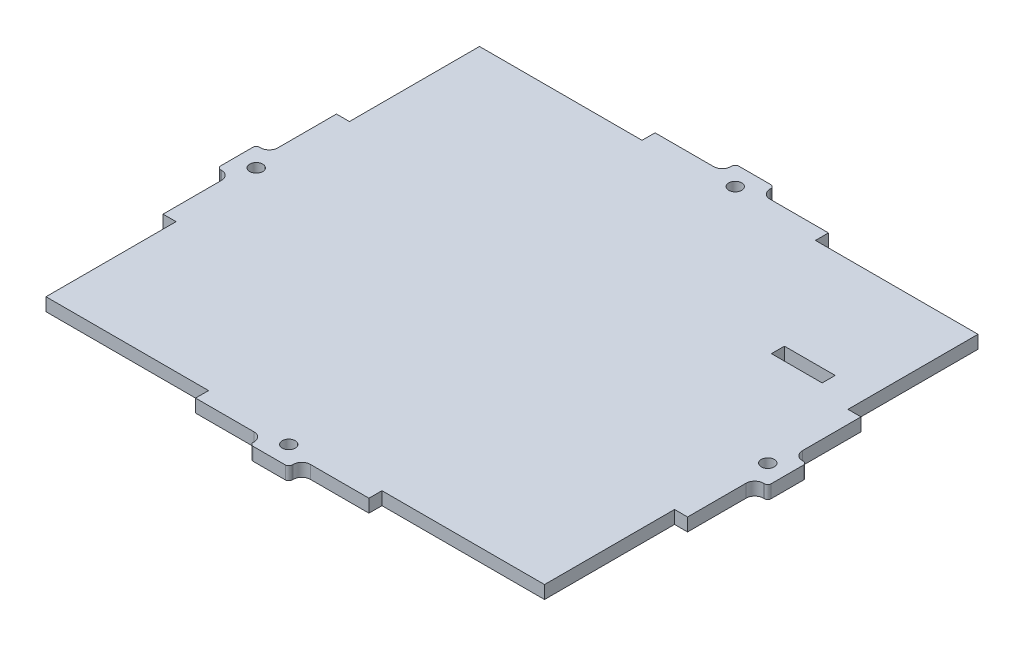
SolidWorks part; units mm, degrees
material "Acrylic (Medium-high impact)"
ref_plane "Plano frontal" through (0, 0, 0) normal (0, 0, 1) x (1, 0, 0)
ref_plane "Plano superior" through (0, 0, 0) normal (0, 1, 0) x (1, 0, 0)
ref_plane "Plano direito" through (0, 0, 0) normal (1, 0, 0) x (0, 0, -1)
sketch "Esboço1" plane through (0, 0, 0) normal (0, 1, 0) x (1, 0, 0)
  line L1 (-57.5, -50) -> (57.5, -50)
  line L2 (-57.5, -50) -> (-57.5, 50)
  line L3 (-57.5, 50) -> (57.5, 50)
  line L4 (57.5, -50) -> (57.5, 50)
  line L5 (-57.5, -50) -> (57.5, 50) construction
  line L6 (-57.5, 50) -> (57.5, -50) construction
  point P0 (0, 0)
  dimension "D1" = 115
  dimension "D2" = 100
extrude "Ressalto-extrusão1" add sketch "Esboço1" along normal mid plane 3
sketch "Esboço4" plane through (0, 1.5, 0) normal (0, 1, 0) x (1, 0, 0)
  line L5 (0, -1.65) -> (0, 1.65) construction
  line L21 (6.5, 53) -> (20, 53)
  line L26 (-3.7, 56) -> (3.7, 56)
  line L27 (-4.5, 55.2) -> (-4.5, 55)
  line L33 (-63.5, 3.7) -> (-63.5, -3.7)
  line L42 (57.5, 50) -> (-57.5, 50) construction
  line L43 (-20, 50) -> (20, 50)
  line L44 (-20, 50) -> (-20, 53)
  line L45 (-20, 53) -> (-6.5, 53)
  line L46 (20, 50) -> (20, 53)
  line L48 (4.5, 55.2) -> (4.5, 55)
  line L49 (-1.65, 0) -> (1.65, 0) construction
  line L50 (4.5, -55.2) -> (4.5, -55)
  line L51 (20, -50) -> (20, -53)
  line L52 (-20, -53) -> (-6.5, -53)
  line L53 (-20, -50) -> (-20, -53)
  line L54 (-20, -50) -> (20, -50)
  line L55 (-4.5, -55.2) -> (-4.5, -55)
  line L56 (-3.7, -56) -> (3.7, -56)
  line L57 (6.5, -53) -> (20, -53)
  line L58 (57.5, -50) -> (57.5, 50) construction
  line L59 (57.5, 20) -> (60.5, 20)
  line L60 (57.5, 20) -> (57.5, -20)
  line L61 (57.5, -20) -> (60.5, -20)
  line L62 (60.5, 20) -> (60.5, 6.5)
  line L63 (60.5, -6.5) -> (60.5, -20)
  line L64 (62.5, 4.5) -> (62.7, 4.5)
  line L66 (62.5, -4.5) -> (62.7, -4.5)
  line L67 (63.5, 3.7) -> (63.5, -3.7)
  line L77 (-62.5, -4.5) -> (-62.7, -4.5)
  line L91 (-62.5, 4.5) -> (-62.7, 4.5)
  line L92 (-60.5, -6.5) -> (-60.5, -20)
  line L93 (-60.5, 20) -> (-60.5, 6.5)
  line L94 (-57.5, -20) -> (-60.5, -20)
  line L95 (-57.5, 20) -> (-57.5, -20)
  line L96 (-57.5, 20) -> (-60.5, 20)
  circle A6 centre (0, 51.5) radius 1.5 construction
  arc A7 (6.5, 53) -> (4.5, 55) centre (6.5, 55) cw
  arc A8 (-4.5, 55) -> (-6.5, 53) centre (-6.5, 55) cw
  circle A9 centre (0, -51.5) radius 1.5 construction
  arc A10 (-4.5, -55) -> (-6.5, -53) centre (-6.5, -55) ccw
  arc A11 (6.5, -53) -> (4.5, -55) centre (6.5, -55) ccw
  arc A12 (60.5, -6.5) -> (62.5, -4.5) centre (62.5, -6.5) cw
  arc A13 (62.5, 4.5) -> (60.5, 6.5) centre (62.5, 6.5) cw
  arc A18 (-62.5, 4.5) -> (-60.5, 6.5) centre (-62.5, 6.5) ccw
  arc A19 (-60.5, -6.5) -> (-62.5, -4.5) centre (-62.5, -6.5) ccw
  arc A20 (-63.5, -3.7) -> (-62.7, -4.5) centre (-62.7, -3.7) ccw
  arc A21 (-63.5, 3.7) -> (-62.7, 4.5) centre (-62.7, 3.7) cw
  arc A22 (-4.5, -55.2) -> (-3.7, -56) centre (-3.7, -55.2) ccw
  arc A23 (4.5, -55.2) -> (3.7, -56) centre (3.7, -55.2) cw
  arc A24 (62.7, -4.5) -> (63.5, -3.7) centre (62.7, -3.7) ccw
  arc A25 (62.7, 4.5) -> (63.5, 3.7) centre (62.7, 3.7) cw
  arc A26 (3.7, 56) -> (4.5, 55.2) centre (3.7, 55.2) cw
  arc A27 (-3.7, 56) -> (-4.5, 55.2) centre (-3.7, 55.2) ccw
  point P16 (63.5, 0)
  point P20 (60.5, 4.5)
  point P21 (57.5, 0)
  point P36 (-60.5, 4.5)
  point P39 (-63.5, -4.5)
  point P42 (0, 50)
  point P51 (4.5, 53)
  point P70 (4.5, -53)
  point P73 (-63.5, 4.5)
  point P76 (-4.5, -56)
  point P79 (4.5, -56)
  point P82 (63.5, -4.5)
  point P85 (63.5, 4.5)
  point P88 (4.5, 56)
  point P91 (-4.5, 56)
  dimension "D2" = 9
  dimension "D6" = 2
  dimension "D8" = 3
  dimension "D9" = 3
  dimension "D11" = 2
  dimension "D7" = 0.8
  dimension "D3" = 40
  dimension "D4" = 9
  dimension "D5" = 3
  dimension "D10" = 3
extrude "Ressalto-extrusão2" add sketch "Esboço4" against normal through all
sketch "Esboço2" plane through (0, 1.5, 0) normal (0, 1, 0) x (1, 0, 0)
  line L27 (0, -1.65) -> (0, 1.65) construction
  line L32 (-20, -53) -> (-6.5, -53) construction
  line L51 (63.5, -3.7) -> (63.5, 3.7) construction
  line L90 (-3.7, -56) -> (3.7, -56) construction
  line L91 (-1.65, 0) -> (1.65, 0) construction
  circle A8 centre (0, -51.5) radius 1.5
  circle A9 centre (0, 51.5) radius 1.5
  circle A11 centre (59, 0) radius 1.5
  circle A14 centre (-59, 0) radius 1.5
  dimension "D1" = 3
  dimension "D2" = 3
  dimension "D3" = 3
extrude "Corte-extrusão1" cut sketch "Esboço2" against normal through all
sketch "Sketch2" plane through (0, 0, 0) normal (0, 1, 0) x (1, 0, 0)
  line L8 (32.2, 2.3) -> (57.5, 2.3) construction
  line L25 (32.2, 28.4) -> (57.5, 28.4) construction
  line L43 (32.2, 28.4) -> (32.2, -23.8) construction
  line L44 (32.2, -23.8) -> (57.5, -23.8) construction
  line L45 (57.5, 28.4) -> (57.5, -23.8) construction
  line L46 (32.2, -2.3) -> (57.5, -2.3) construction
  line L47 (44.85, 2.3) -> (44.85, -2.3) construction
  line L48 (57.5, 20) -> (57.5, 50) construction
  line L49 (38.3, 25.1) -> (48.5, 25.1) construction
  line L50 (38.3, 25.1) -> (38.3, 22.5) construction
  line L51 (38.3, 22.5) -> (48.5, 22.5) construction
  line L52 (48.5, 25.1) -> (48.5, 22.5) construction
  line L54 (37.55, 25.3) -> (49.25, 25.3)
  line L55 (37.55, 25.3) -> (37.55, 22.3)
  line L56 (37.55, 22.3) -> (49.25, 22.3)
  line L57 (49.25, 25.3) -> (49.25, 22.3)
  point P10 (44.85, 0)
  point P15 (37.55, 23.8)
  point P16 (38.3, 23.8)
  point P17 (43.4, 25.1)
  point P24 (43.4, 25.3)
  dimension "D10" = 11.7
  dimension "D1" = 52.2
  dimension "D2" = 25.3
  dimension "D4" = 21.5
  dimension "D5" = 3.3
  dimension "D6" = 10.2
  dimension "D7" = 2.6
  dimension "D8" = 9
  dimension "D9" = 26.1
  dimension "D3" = 4.6
  dimension "D11" = 0.2
  dimension "D12" = 0.75
extrude "Cut-Extrude3" cut sketch "Sketch2" against normal through all both and the other way through all
